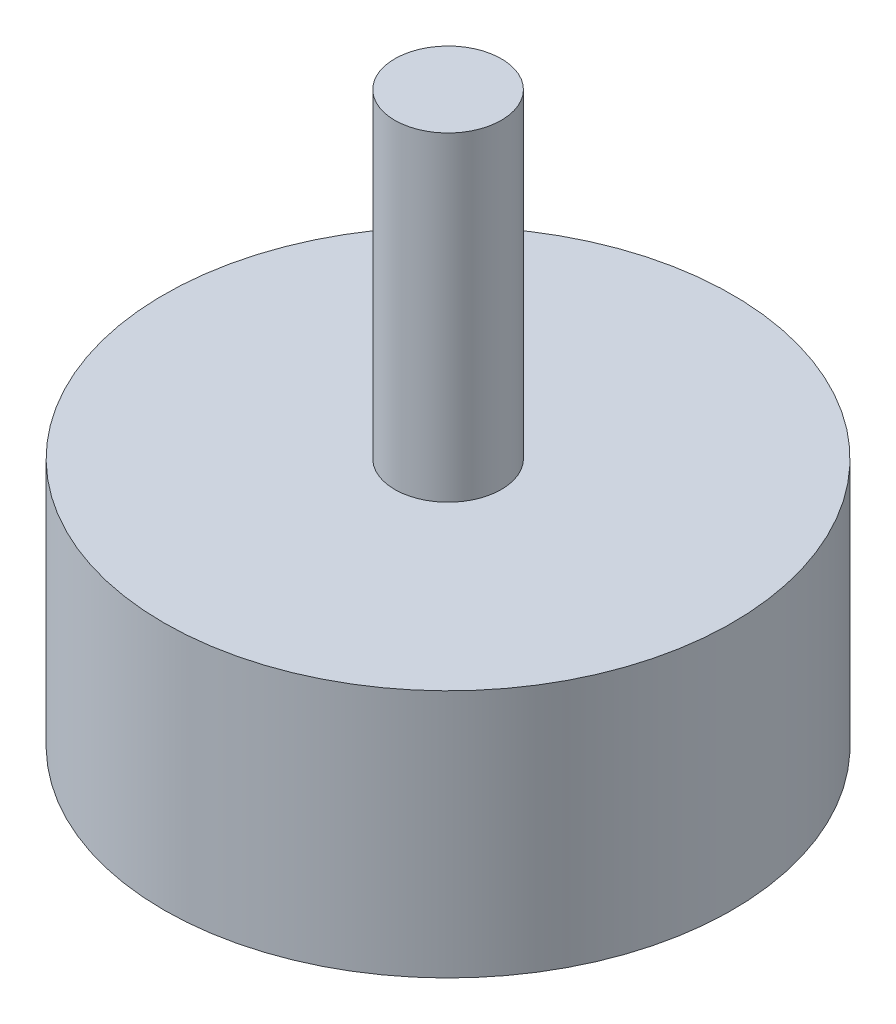
SolidWorks part; units mm, degrees
material "Rubber"
ref_plane "Front Plane" through (0, 0, 0) normal (0, 0, 1) x (1, 0, 0)
ref_plane "Top Plane" through (0, 0, 0) normal (0, 1, 0) x (1, 0, 0)
ref_plane "Right Plane" through (0, 0, 0) normal (1, 0, 0) x (0, 0, -1)
sketch "Sketch1" plane through (0, 0, 0) normal (0, 1, 0) x (1, 0, 0)
  circle A0 centre (0, 0) radius 25.4
  dimension "D1" = 50.8
extrude "Boss-Extrude1" add sketch "Sketch1" along normal mid plane 22.225
sketch "Sketch2" plane through (0, 11.1125, 0) normal (0, 1, 0) x (1, 0, 0)
  circle A0 centre (0, 0) radius 4.7625
extrude "Boss-Extrude2" add sketch "Sketch2" along normal blind 28.575
mirror "Mirror1" about plane through (0, 0, 0) normal (0, 1, 0) of "Boss-Extrude2"
sketch "Sketch3" plane through (0, -39.6875, 0) normal (0, -1, 0) x (-1, 0, 0)
  circle A0 centre (0, 0) radius 4.7625
extrude "Cut-Extrude1" cut sketch "Sketch3" against normal offset from surface (15.875 mm away) 12.7 up to face at (0, -11.1125, 4.7625)
